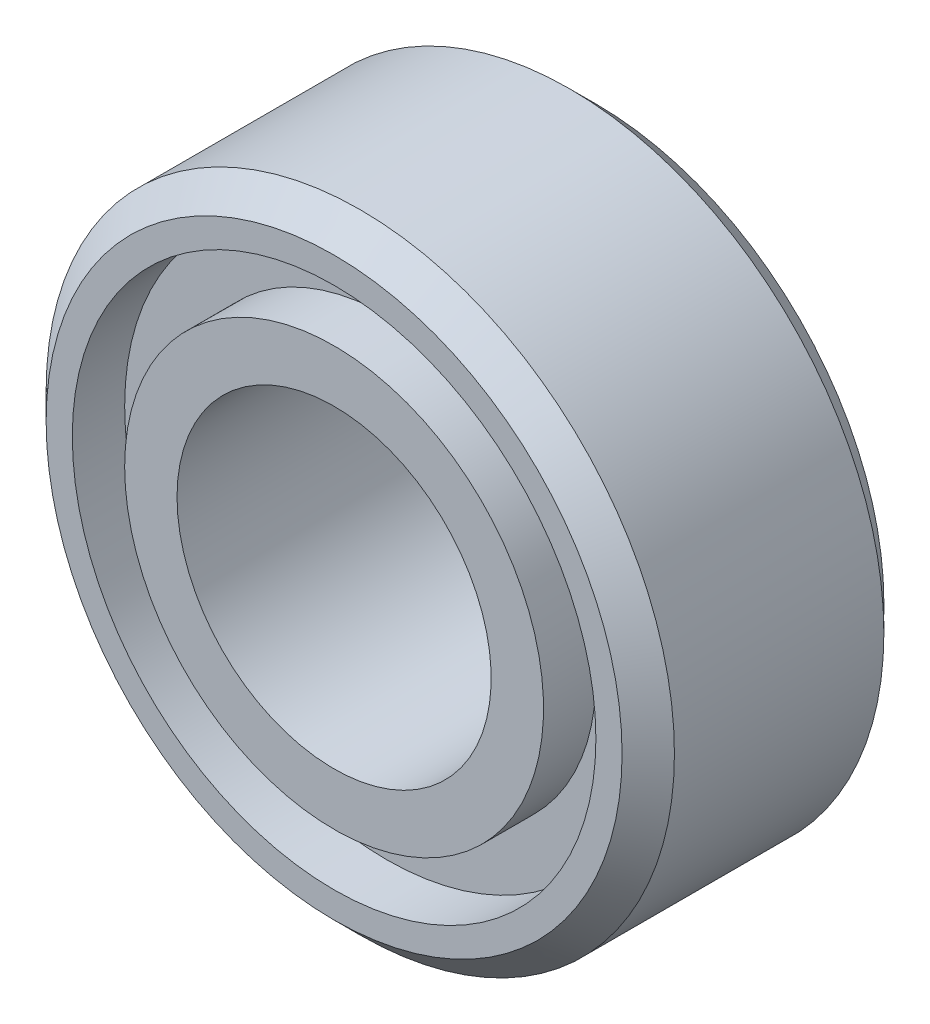
SolidWorks part; units mm, degrees
ref_plane "Front Plane" through (0, 0, 0) normal (0, 0, 1) x (1, 0, 0)
ref_plane "Top Plane" through (0, 0, 0) normal (0, 1, 0) x (1, 0, 0)
ref_plane "Right Plane" through (0, 0, 0) normal (1, 0, 0) x (0, 0, -1)
ref_plane "Plane1" through (0, 0, 0) normal (0, -1, 0) x (1, 0, 0)
sketch "Sketch1" plane through (0, 0, 0) normal (0, -1, 0) x (1, 0, 0)
  line L0 (3, -0.25) -> (2.75, 0)
  line L1 (2.75, 0) -> (2.5, 0)
  line L2 (2.5, 0) -> (2.5, -0.5)
  line L3 (2.5, -0.5) -> (2, -0.5)
  line L4 (2, -0.5) -> (2, 0)
  line L5 (2, 0) -> (1.5, 0)
  line L6 (1.5, 0) -> (1.5, -2.5)
  line L7 (1.5, -2.5) -> (2, -2.5)
  line L8 (2, -2.5) -> (2, -2)
  line L9 (2, -2) -> (2.5, -2)
  line L10 (2.5, -2) -> (2.5, -2.5)
  line L11 (2.5, -2.5) -> (2.75, -2.5)
  line L12 (2.75, -2.5) -> (3, -2.25)
  line L13 (3, -2.25) -> (3, -0.25)
  line L14 (0, 2.5) -> (0, -2.5) construction
  dimension "D1" = 3
  dimension "D2" = 0.25
  dimension "D3" = 4
  dimension "D4" = 2.5
  dimension "D5" = 6
  dimension "D7" = 0.5
  dimension "D8" = 45
  dimension "D9" = 5
revolve "Revolve1" add sketch "Sketch1" angle 360 about L14
